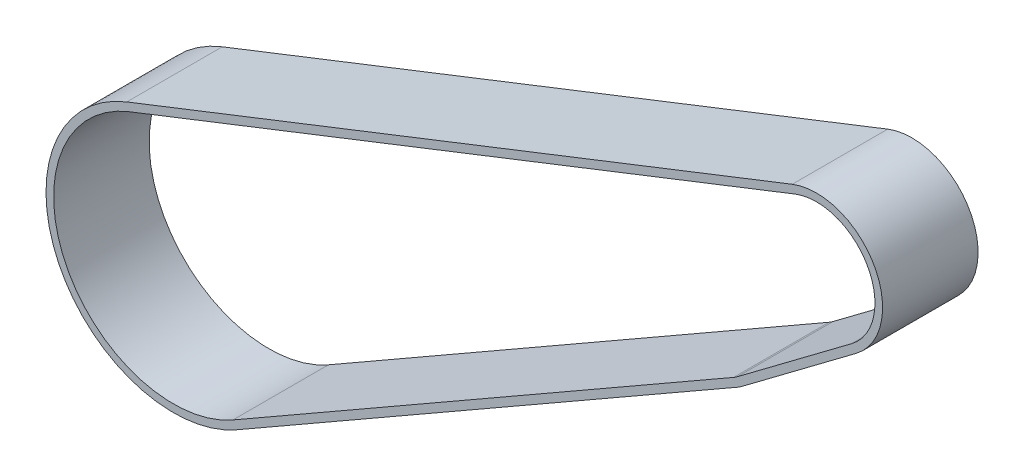
SolidWorks part; units mm, degrees
material "NEOPRENE"
ref_plane "Front Plane" through (0, 0, 0) normal (0, 0, 1) x (1, 0, 0)
ref_plane "Top Plane" through (0, 0, 0) normal (0, 1, 0) x (1, 0, 0)
ref_plane "Right Plane" through (0, 0, 0) normal (1, 0, 0) x (0, 0, -1)
sketch "Sketch1" plane through (0, 0, 0) normal (0, 0, 1) x (1, 0, 0)
  line L0 (0, 0) -> (1, 0) construction
  line L1 (0, 0) -> (0, 1) construction
  line L2 (-340.252, -14.6744) -> (-444.7646, -55.7334)
  line L3 (-428.5361, -89.5391) -> (-349.9049, -44.436)
  line L4 (-349.2889, -44.0304) -> (-331.372, -30.5848)
  arc A0 (-331.372, -30.5848) -> (-340.252, -14.6744) centre (-336.8903, -23.2315) ccw
  arc A1 (-444.7646, -55.7334) -> (-428.5361, -89.5391) centre (-437.8903, -73.2315) ccw
  arc A2 (-349.9049, -44.436) -> (-349.2889, -44.0304) centre (-352.8903, -39.2315) ccw
extrude "Extrude-Thin1" add sketch "Sketch1" along normal blind 15 thin contours L2 A1 L3 A2 L4 A0
